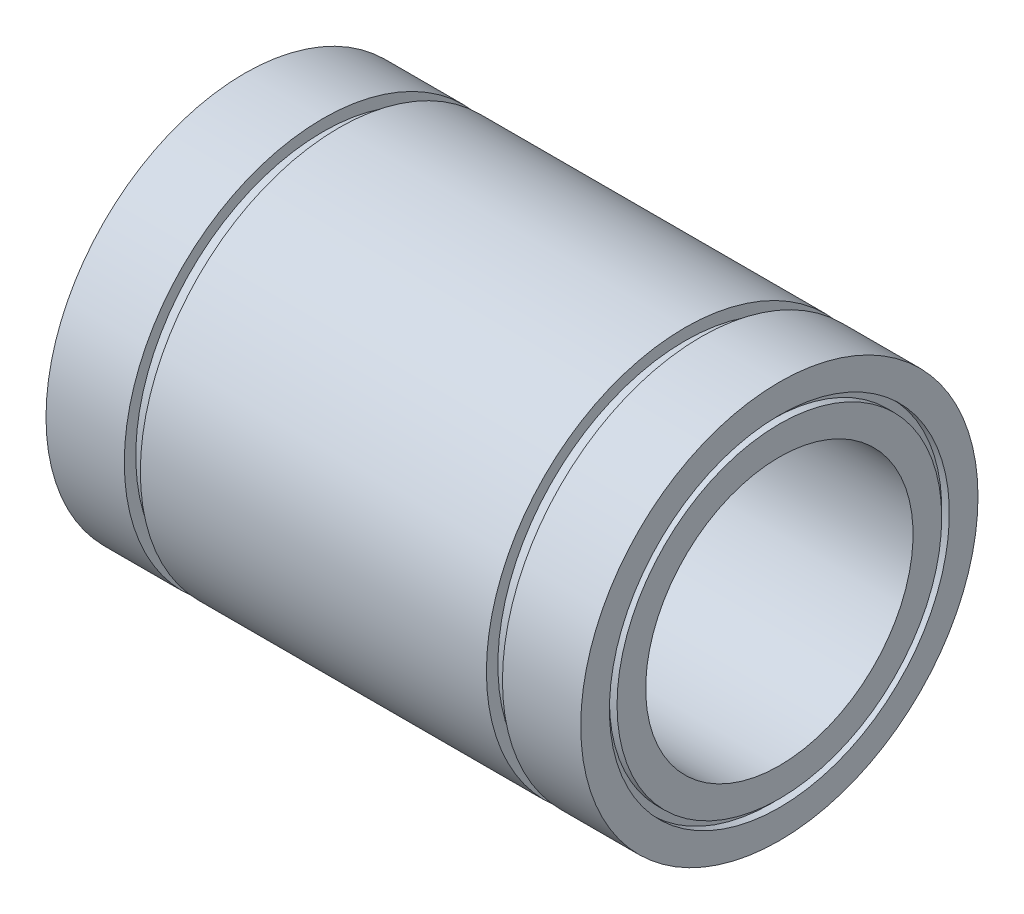
SolidWorks part; units mm, degrees
material "Ст3сп ГОСТ 535-2005"
ref_plane "Plano frontal" through (0, 0, 0) normal (0, 0, 1) x (1, 0, 0)
ref_plane "Plano superior" through (0, 0, 0) normal (0, 1, 0) x (1, 0, 0)
ref_plane "Plano direito" through (0, 0, 0) normal (1, 0, 0) x (0, 0, -1)
sketch "Esboço1" plane through (0, 0, 0) normal (0, 0, 1) x (1, 0, 0)
  line L0 (-35, 26) -> (-24.75, 26)
  line L1 (-24.75, 26) -> (-24.75, 24.5)
  line L2 (-24.75, 24.5) -> (-22.65, 24.5)
  line L3 (-22.65, 24.5) -> (-22.65, 26)
  line L4 (-22.65, 26) -> (22.65, 26)
  line L5 (22.65, 26) -> (22.65, 24.5)
  line L6 (22.65, 24.5) -> (24.75, 24.5)
  line L7 (24.75, 24.5) -> (24.75, 26)
  line L8 (24.75, 26) -> (35, 26)
  line L9 (35, 26) -> (35, 22.25)
  line L10 (35, 17.5) -> (-35, 17.5)
  line L11 (-35, 17.5) -> (-35, 21.25)
  line L12 (0, 17.5) -> (0, 0) construction
  line L13 (0, 0) -> (-86.5, 0) construction
  line L14 (-35, 22.25) -> (-35, 26)
  line L15 (-35, 22.25) -> (-34, 22.25)
  line L16 (35, 21.25) -> (35, 17.5)
  line L17 (-34, 22.25) -> (-34, 21.25)
  line L18 (-34, 21.25) -> (-35, 21.25)
  line L19 (35, 22.25) -> (34, 22.25)
  line L21 (35, 21.25) -> (34, 21.25)
  line L22 (34, 22.25) -> (34, 21.25)
  dimension "D1" = 70
  dimension "D2" = 49.5
  dimension "D3" = 2.1
  dimension "D4" = 35
  dimension "D5" = 52
  dimension "D6" = 49
  dimension "D7" = 1
  dimension "D8" = 1
  dimension "D9" = 1
  dimension "D10" = 1
revolve "Revolução1" add sketch "Esboço1" angle 360 about L13
